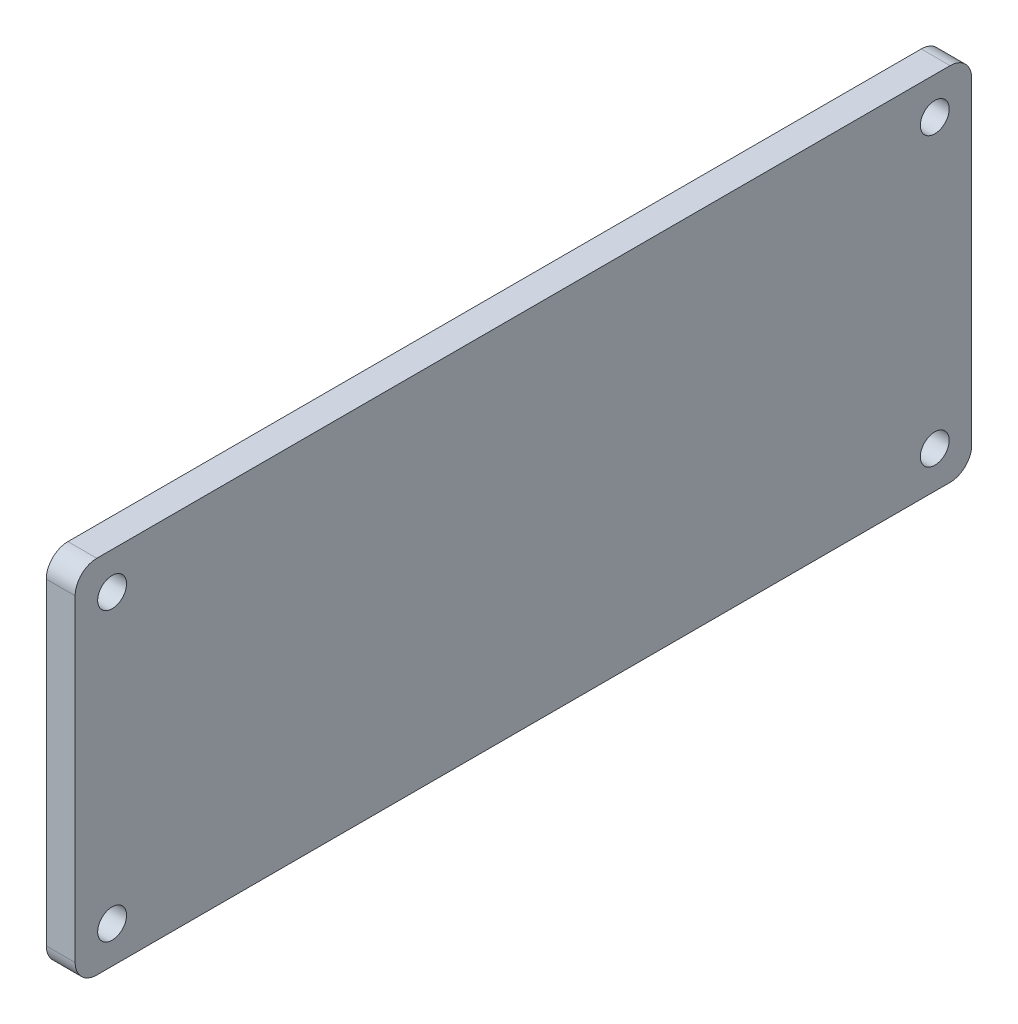
SolidWorks part; units mm, degrees
ref_plane "Front Plane" through (0, 0, 0) normal (0, 0, 1) x (1, 0, 0)
ref_plane "Top Plane" through (0, 0, 0) normal (0, 1, 0) x (1, 0, 0)
ref_plane "Right Plane" through (0, 0, 0) normal (1, 0, 0) x (0, 0, -1)
sketch "Sketch1" plane through (0, 0, 0) normal (1, 0, 0) x (0, 0, -1)
  line L0 (30.6107, 12.0607) -> (28.4893, 9.9393) construction
  line L1 (-29.55, -12.5) -> (29.55, -12.5)
  line L2 (-31.05, -11) -> (-31.05, 11)
  line L3 (-29.55, 12.5) -> (29.55, 12.5)
  line L4 (31.05, -11) -> (31.05, 11)
  line L5 (-31.05, -12.5) -> (31.05, 12.5) construction
  line L6 (-31.05, 12.5) -> (31.05, -12.5) construction
  line L7 (0, 13.75) -> (0, -13.75) construction
  line L8 (-30.6107, 12.0607) -> (-28.4893, 9.9393) construction
  line L9 (34.155, 0) -> (-34.155, 0) construction
  arc A0 (-31.05, 11) -> (-29.55, 12.5) centre (-29.55, 11) cw
  arc A1 (-29.55, -12.5) -> (-31.05, -11) centre (-29.55, -11) cw
  arc A2 (29.55, -12.5) -> (31.05, -11) centre (29.55, -11) ccw
  arc A3 (29.55, 12.5) -> (31.05, 11) centre (29.55, 11) cw
  circle A4 centre (28.4893, 9.9393) radius 1
  circle A5 centre (-28.4893, 9.9393) radius 1
  circle A6 centre (28.4893, -9.9393) radius 1
  circle A7 centre (-28.4893, -9.9393) radius 1
  point P0 (0, 0)
  dimension "D3" = 1.5
  dimension "D4" = 1.5
  dimension "D5" = 1.5
  dimension "D6" = 1.5
  dimension "D8" = 2
  dimension "D1" = 25
  dimension "D2" = 62.1
  dimension "D7" = 3
extrude "Boss-Extrude1" add sketch "Sketch1" along normal blind 2 contours L3 A3 L4 A2 L1 A1 L2 A0 | A5 | A7 | A6 | A4
